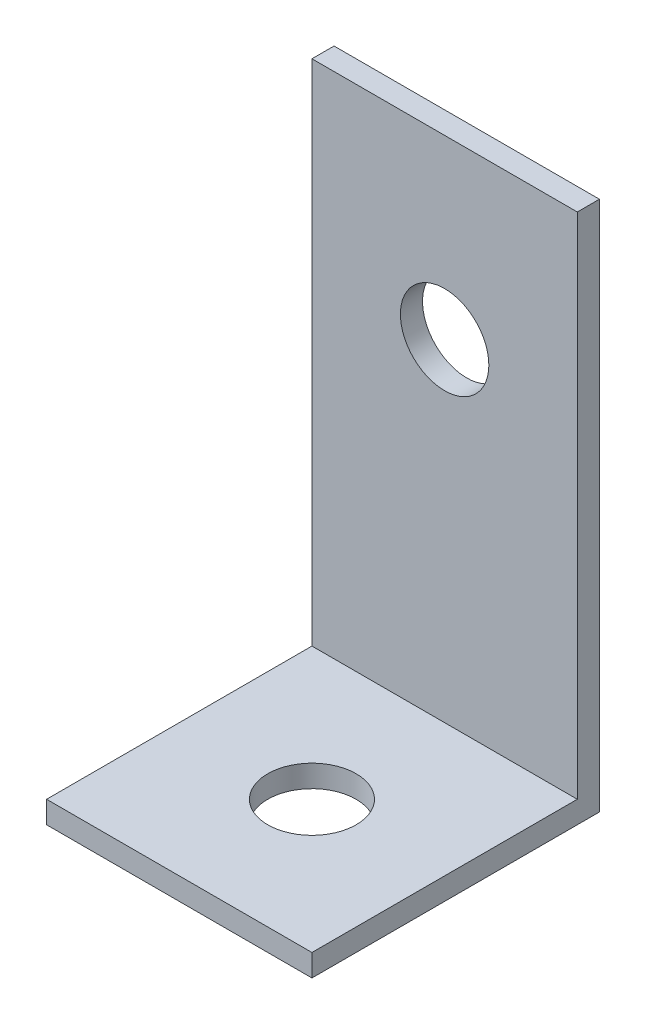
SolidWorks part; units mm, degrees
ref_plane "Front Plane" through (0, 0, 0) normal (0, 0, 1) x (1, 0, 0)
ref_plane "Top Plane" through (0, 0, 0) normal (0, 1, 0) x (1, 0, 0)
ref_plane "Right Plane" through (0, 0, 0) normal (1, 0, 0) x (0, 0, -1)
sketch "Sketch1" plane through (0, 0, 0) normal (0, 0, 1) x (1, 0, 0)
  line L1 (-9.525, 19.05) -> (9.525, 19.05)
  line L2 (-9.525, 19.05) -> (-9.525, -19.05)
  line L3 (-9.525, -19.05) -> (9.525, -19.05)
  line L4 (9.525, 19.05) -> (9.525, -19.05)
  line L5 (-9.525, 19.05) -> (9.525, -19.05) construction
  line L6 (-9.525, -19.05) -> (9.525, 19.05) construction
  circle A2 centre (0, 6.35) radius 3.175
  point P1 (0, 0)
extrude "Boss-Extrude1" add sketch "Sketch1" along normal mid plane 1.5875
sketch "Sketch2" plane through (0, -19.05, 0) normal (0, -1, 0) x (1, 0, 0)
  line L0 (-9.525, 0.7937) -> (9.525, 0.7937)
  line L1 (-9.525, 0.7937) -> (-9.525, 19.8438)
  line L2 (9.525, 0.7937) -> (9.525, 19.8438)
  line L3 (-9.525, 19.8438) -> (9.525, 19.8438)
  circle A1 centre (0, 10.3187) radius 3.175
extrude "Boss-Extrude2" add sketch "Sketch2" against normal blind 1.5875
